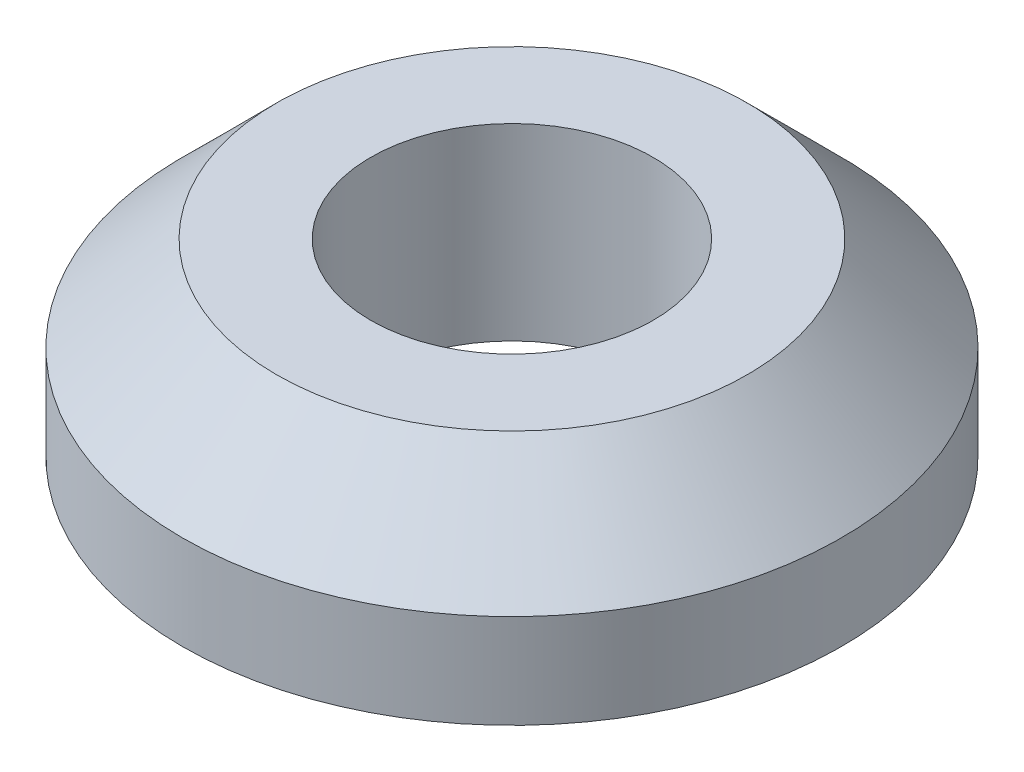
SolidWorks part; units mm, degrees
ref_plane "Front Plane" through (0, 0, 0) normal (0, 0, 1) x (1, 0, 0)
ref_plane "Top Plane" through (0, 0, 0) normal (0, 1, 0) x (1, 0, 0)
ref_plane "Right Plane" through (0, 0, 0) normal (1, 0, 0) x (0, 0, -1)
sketch "Sketch1" plane through (0, 0, 0) normal (0, 1, 0) x (1, 0, 0)
  circle A0 centre (0, 0) radius 3.5
  dimension "D1" = 7
extrude "Boss-Extrude1" add sketch "Sketch1" along normal blind 2
chamfer "Chamfer1" distance 1 angle 45 1 edges at (0, 2, 3.5)
sketch "Sketch2" plane through (0, 2, 0) normal (0, 1, 0) x (1, 0, 0)
  circle A0 centre (0, 0) radius 1.5
  dimension "D1" = 3
extrude "Cut-Extrude1" cut sketch "Sketch2" against normal blind 2
